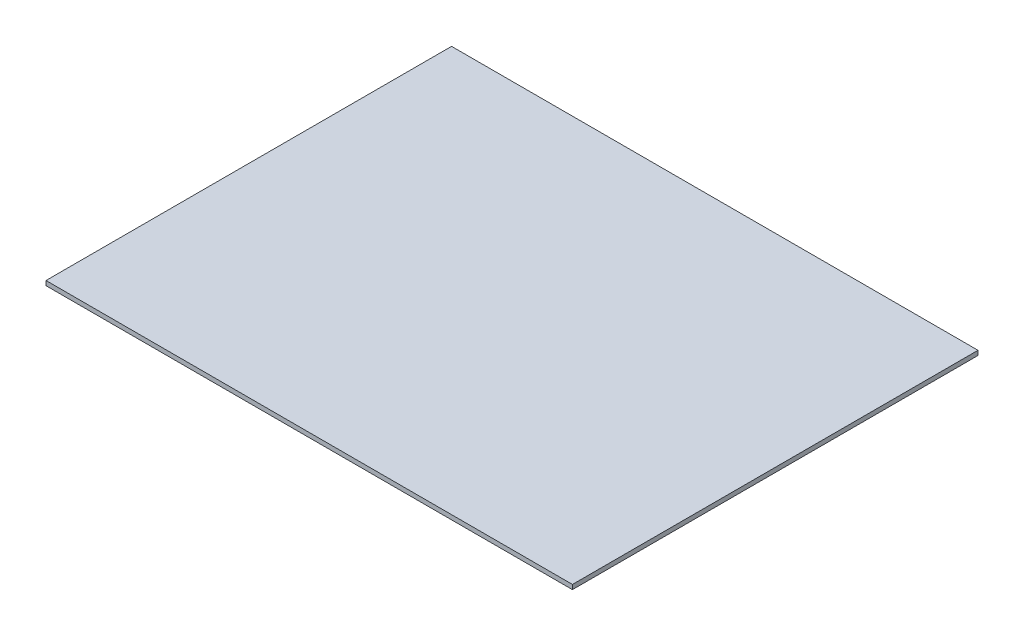
SolidWorks part; units mm, degrees
ref_plane "Спереди" through (0, 0, 0) normal (0, 0, 1) x (1, 0, 0)
ref_plane "Сверху" through (0, 0, 0) normal (0, 1, 0) x (1, 0, 0)
ref_plane "Справа" through (0, 0, 0) normal (1, 0, 0) x (0, 0, -1)
sketch "Эскиз1" plane through (0, 0, 0) normal (0, 1, 0) x (1, 0, 0)
  line L1 (-233, -179.5) -> (233, -179.5)
  line L2 (-233, -179.5) -> (-233, 179.5)
  line L3 (-233, 179.5) -> (233, 179.5)
  line L4 (233, -179.5) -> (233, 179.5)
  line L5 (-233, -179.5) -> (233, 179.5) construction
  line L6 (-233, 179.5) -> (233, -179.5) construction
  point P0 (0, 0)
  dimension "D1" = 359
  dimension "D2" = 466
extrude "Бобышка-Вытянуть1" add sketch "Эскиз1" along normal blind 4
